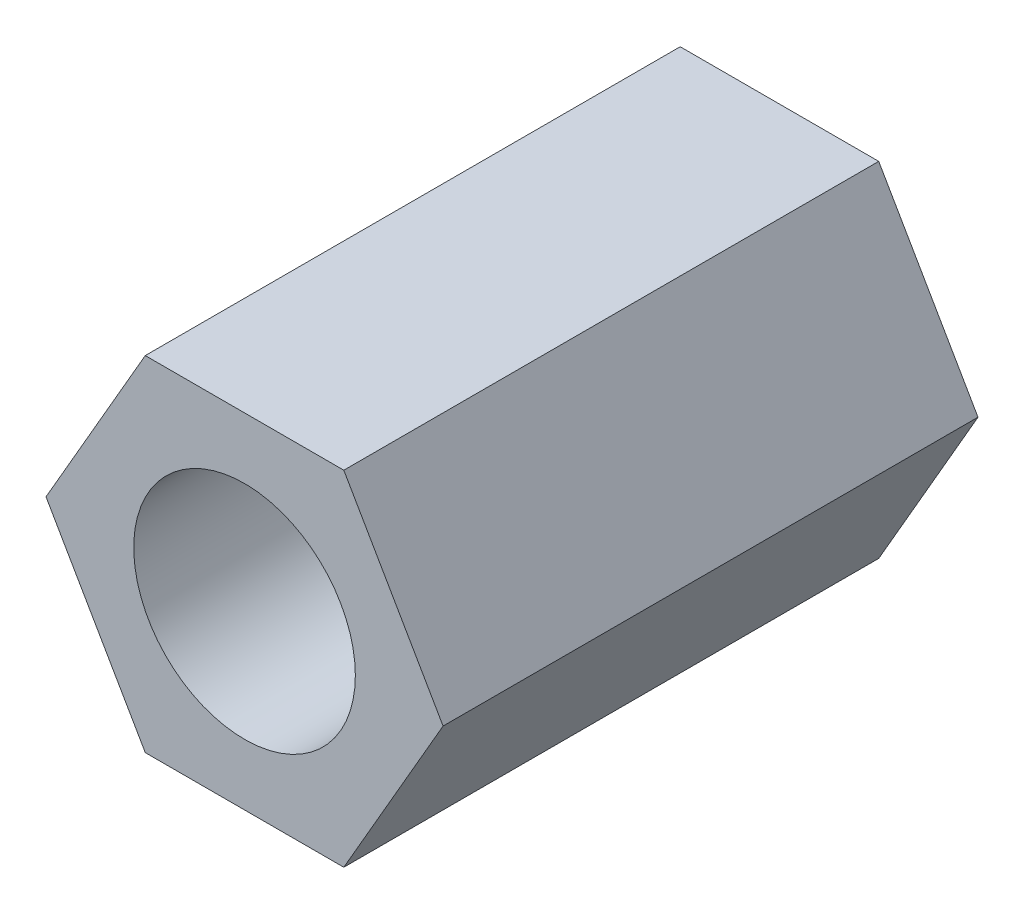
SolidWorks part; units mm, degrees
ref_plane "Front Plane" through (0, 0, 0) normal (0, 0, 1) x (1, 0, 0)
ref_plane "Top Plane" through (0, 0, 0) normal (0, 1, 0) x (1, 0, 0)
ref_plane "Right Plane" through (0, 0, 0) normal (1, 0, 0) x (0, 0, -1)
sketch "Sketch1" plane through (0, 0, 0) normal (0, 0, 1) x (1, 0, 0)
  line L0 (-2.5981, 0) -> (2.5981, 0) construction
  line L1 (-1.299, -2.25) -> (1.299, -2.25)
  line L2 (-1.299, -2.25) -> (-1.299, 2.25) construction
  line L3 (-1.299, 2.25) -> (1.299, 2.25)
  line L4 (1.299, -2.25) -> (1.299, 2.25) construction
  line L5 (-1.299, -2.25) -> (1.299, 2.25) construction
  line L6 (-1.299, 2.25) -> (1.299, -2.25) construction
  line L7 (-2.5981, 0) -> (-1.299, 2.25)
  line L8 (-2.5981, 0) -> (-1.299, -2.25)
  line L9 (1.299, -2.25) -> (2.5981, 0)
  line L10 (2.5981, 0) -> (1.299, 2.25)
  circle A0 centre (0, 0) radius 1.45
  point P0 (0, 0)
  point P9 (0, 0)
  dimension "D4" = 2.9
  dimension "D1" = 4.5
  dimension "D2" = 4.5
  dimension "D3" = 120
extrude "Boss-Extrude1" add sketch "Sketch1" along normal blind 7
